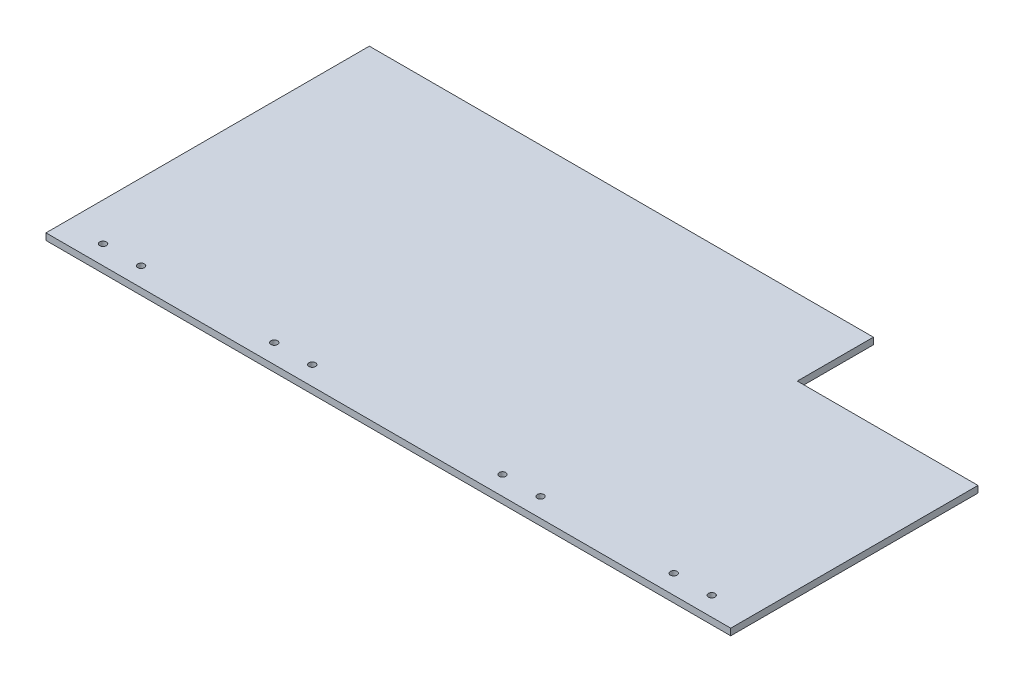
SolidWorks part; units mm, degrees
ref_plane "Front Plane" through (0, 0, 0) normal (0, 0, 1) x (1, 0, 0)
ref_plane "Top Plane" through (0, 0, 0) normal (0, 1, 0) x (1, 0, 0)
ref_plane "Right Plane" through (0, 0, 0) normal (1, 0, 0) x (0, 0, -1)
sketch "Sketch1" plane through (0, 0, 0) normal (0, 1, 0) x (1, 0, 0)
  line L1 (0, 0) -> (360, 0)
  line L2 (0, 0) -> (0, 170)
  line L3 (0, 170) -> (360, 170)
  line L4 (360, 0) -> (360, 170)
  dimension "D1" = 170
  dimension "D2" = 360
extrude "Boss-Extrude1" add sketch "Sketch1" along normal blind 3.5
sketch "Sketch2" plane through (0, 3.5, 0) normal (0, 1, 0) x (1, 0, 0)
  line L0 (0, 10) -> (360, 10) construction
  line L1 (0, 170) -> (0, 0) construction
  line L2 (360, 0) -> (360, 170) construction
  line L3 (0, 0) -> (360, 0) construction
  line L4 (180, 170) -> (180, 0) construction
  line L5 (360, 170) -> (0, 170) construction
  circle A0 centre (20, 10) radius 1.75
  circle A1 centre (40, 10) radius 1.75
  circle A2 centre (110, 10) radius 1.75
  circle A3 centre (130, 10) radius 1.75
  circle A4 centre (230, 10) radius 1.75
  circle A5 centre (250, 10) radius 1.75
  circle A6 centre (320, 10) radius 1.75
  circle A7 centre (340, 10) radius 1.75
  dimension "D2" = 3.5
  dimension "D3" = 20
  dimension "D5" = 20
  dimension "D7" = 70
  dimension "D1" = 10
  dimension "D4" = 2
  dimension "D6" = 2
extrude "Cut-Extrude1" cut sketch "Sketch2" against normal blind 3.5
sketch "Sketch3" plane through (0, 3.5, 0) normal (0, 1, 0) x (1, 0, 0)
  line L1 (360, 170) -> (265, 170)
  line L2 (360, 170) -> (360, 130)
  line L3 (360, 130) -> (265, 130)
  line L4 (265, 170) -> (265, 130)
  dimension "D1" = 95
  dimension "D2" = 40
extrude "Cut-Extrude2" cut sketch "Sketch3" against normal up to next
